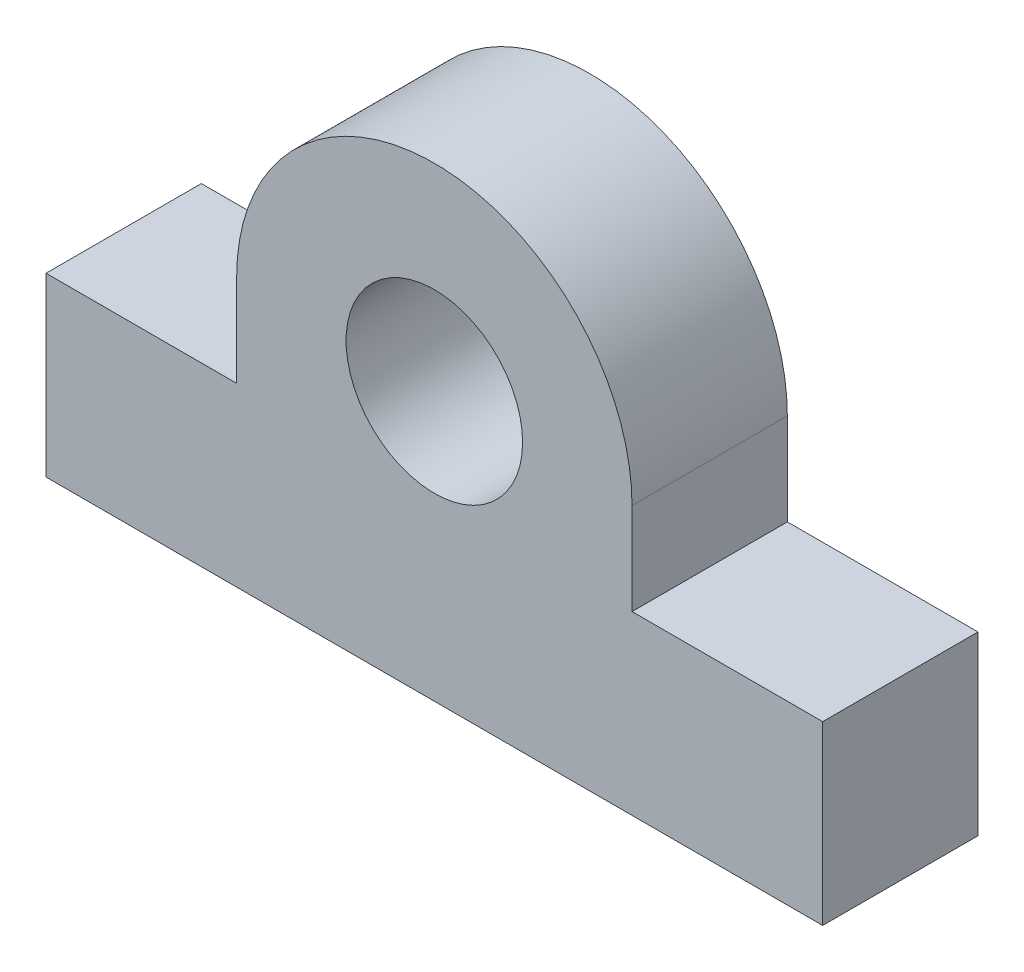
SolidWorks part; units mm, degrees
material "Plain Carbon Steel"
ref_plane "Front Plane" through (0, 0, 0) normal (0, 0, 1) x (1, 0, 0)
ref_plane "Top Plane" through (0, 0, 0) normal (0, 1, 0) x (1, 0, 0)
ref_plane "Right Plane" through (0, 0, 0) normal (1, 0, 0) x (0, 0, -1)
sketch "Sketch1" plane through (0, 0, 0) normal (0, 0, 1) x (1, 0, 0)
  line L0 (-55, 0) -> (55, 0)
  line L1 (55, 0) -> (55, 25)
  line L2 (55, 25) -> (-55, 25) construction
  line L3 (-55, 0) -> (-55, 25)
  line L4 (0, 25) -> (0, 219.9692) construction
  line L5 (-28, 25) -> (-28, 38)
  line L6 (28, 25) -> (28, 38)
  line L7 (-55, 25) -> (-28, 25)
  line L8 (28, 25) -> (55, 25)
  arc A0 (-28, 38) -> (28, 38) centre (0, 38) cw
  circle A1 centre (0, 38) radius 12.5
  point P4 (0, 66)
  dimension "D3" = 28
  dimension "D4" = 25
  dimension "D1" = 25
  dimension "D2" = 110
  dimension "D5" = 66
extrude "Boss-Extrude1" add sketch "Sketch1" along normal mid plane 22
